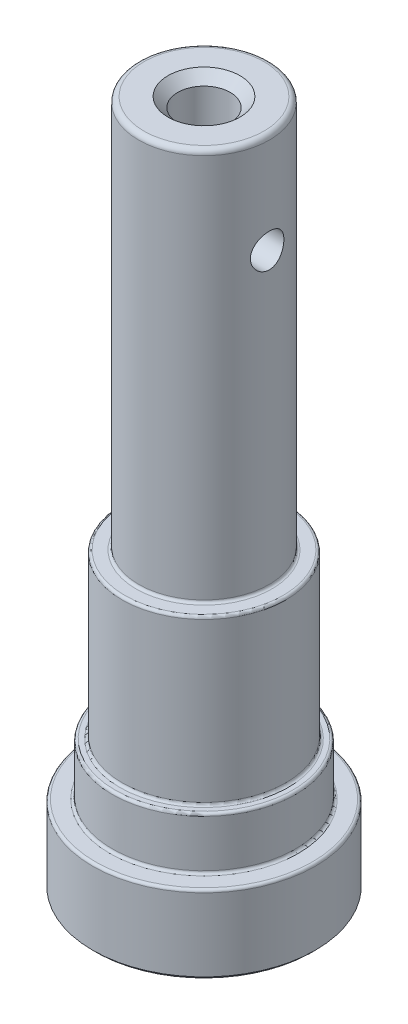
SolidWorks part; units mm, degrees
material "6061 Alloy"
ref_plane "Front Plane" through (0, 0, 0) normal (0, 0, 1) x (1, 0, 0)
ref_plane "Top Plane" through (0, 0, 0) normal (0, 1, 0) x (1, 0, 0)
ref_plane "Right Plane" through (0, 0, 0) normal (1, 0, 0) x (0, 0, -1)
ref_plane "Plane1" through (0, 7.62, 0) normal (0, 1, 0) x (-1, 0, 0)
sketch "Sketch1" plane through (0, 7.62, 0) normal (0, 1, 0) x (-1, 0, 0)
  circle A0 centre (0, 0) radius 10.795
extrude "Extrude1" add sketch "Sketch1" against normal blind 7.62
sketch "Sketch2" plane through (0, 7.62, 0) normal (0, 1, 0) x (-1, 0, 0)
  circle A0 centre (0, 0) radius 8.89
extrude "Extrude2" add sketch "Sketch2" along normal blind 5.08
sketch "Sketch3" plane through (0, 12.7, 0) normal (0, 1, 0) x (-1, 0, 0)
  circle A0 centre (0, 0) radius 7.9375
extrude "Extrude3" add sketch "Sketch3" along normal blind 15.875
sketch "Sketch4" plane through (0, 28.575, 0) normal (0, 1, 0) x (-1, 0, 0)
  circle A0 centre (0, 0) radius 6.3373
  dimension "D1" = 12.6746
extrude "Extrude4" add sketch "Sketch4" along normal blind 38.1
sketch "Sketch5" plane through (0, 0, 0) normal (0, -1, 0) x (1, 0, 0)
  line L0 (3.8125, 5.0038) -> (-3.8125, 5.0038)
  line L1 (-5.0038, 3.8125) -> (-5.0038, -3.8125)
  line L2 (-3.8125, -5.0038) -> (3.8125, -5.0038)
  line L3 (5.0038, -3.8125) -> (5.0038, 3.8125)
  line L4 (3.8125, -3.8125) -> (-3.8125, 3.8125) construction
  line L5 (-3.8125, -3.8125) -> (3.8125, 3.8125) construction
  arc A0 (5.0038, 3.8125) -> (3.8125, 5.0038) centre (3.8125, 3.8125) ccw
  arc A1 (-3.8125, 5.0038) -> (-5.0038, 3.8125) centre (-3.8125, 3.8125) ccw
  arc A2 (-5.0038, -3.8125) -> (-3.8125, -5.0038) centre (-3.8125, -3.8125) ccw
  arc A3 (3.8125, -5.0038) -> (5.0038, -3.8125) centre (3.8125, -3.8125) ccw
  dimension "D1" = 10.0076
  dimension "D2" = 10.0076
extrude "Extrude5" cut sketch "Sketch5" against normal blind 7.62
hole_wizard "1/4-20 Tapped Hole1" positions "Sketch7" profile "Sketch6" tap size "1/4-20" standard "Ansi Inch"
sketch "Sketch7" plane through (0, 66.675, 0) normal (0, 1, 0) x (-1, 0, 0)
  point P0 (0, 0)
sketch "Sketch6" plane through (0, 66.675, 0) normal (1, 0, 0) x (0, 0, 1)
  line L0 (0, 0) -> (0, 15.5038)
  line L1 (0, 15.5038) -> (2.5527, 13.97)
  line L2 (2.5527, 13.97) -> (2.5527, 0.9398)
  line L3 (2.5527, 0.9398) -> (3.4925, 0)
  line L5 (3.4925, 0) -> (0, 0)
  line L6 (-2.5527, 0.9398) -> (-3.4925, 0) construction
  line L10 (0, 15.5038) -> (-2.5527, 13.97) construction
  line L11 (0, -6.35) -> (0, 107.95) construction
  dimension "Tap Drill Dia." = 5.1054
  dimension "Tap Drill Depth" = 13.97
  dimension "Near C'Sink Dia." = 6.985
  dimension "Near C'Sink Angle" = 90
  dimension "Drill Angle" = 118
cosmetic thread "Hole Thread1" parameters "D1"=10.16, "D2"=6.35
chamfer "Chamfer2" distance 0.3048 angle 45 8 edges at (-5.0038, 0, 0) (-4.6549, 0, 4.6549) (-4.6549, 0, -4.6549) (0, 0, 5.0038) (0, 0, -5.0038) (4.6549, 0, 4.6549) (4.6549, 0, -4.6549) (5.0038, 0, 0)
chamfer "Chamfer3" distance 0.3048 angle 45 1 edges at (0, 0, -10.795)
fillet "Fillet1" radius 0.508 1 edges at (0, 66.675, 6.3373)
fillet "Fillet2" radius 0.254 3 edges at (0, 28.575, 6.3373) (0, 12.7, 7.9375) (0, 7.62, -8.89)
fillet "Fillet3" radius 0.254 3 edges at (0, 28.575, 7.9375) (0, 12.7, 8.89) (0, 7.62, -10.795)
sketch "Sketch10" plane through (0, 0, 0) normal (1, 0, 0) x (0, 0, -1)
  line L2 (5.8293, 66.675) -> (-5.8293, 66.675) construction
  circle A0 centre (0, 56.896) radius 1.6256
  dimension "D1" = 3.2512
  dimension "D2" = 9.779
extrude "Extrude6" cut sketch "Sketch10" along normal through all and the other way through all
hole_wizard "Y (0.404) Diameter Hole1" positions "Sketch12" profile "Sketch11" hole size "Y" standard "ANSI Inch"
sketch "Sketch12" plane through (0, 0, 0) normal (0, -1, 0) x (1, 0, 0)
  point P0 (0, 0)
sketch "Sketch11" plane through (0, 0, 0) normal (1, 0, 0) x (0, 0, -1)
  line L0 (0, 0) -> (0, 10.4489)
  line L1 (0, 10.4489) -> (5.1308, 7.366)
  line L2 (5.1308, 7.366) -> (5.1308, 0)
  line L5 (5.1308, 0) -> (0, 0)
  line L10 (0, 10.4489) -> (-5.1308, 7.366) construction
  line L11 (0, -6.35) -> (0, 107.95) construction
  dimension "Hole Dia." = 10.2616
  dimension "Hole Depth" = 7.366
  dimension "Drill Angle" = 118
